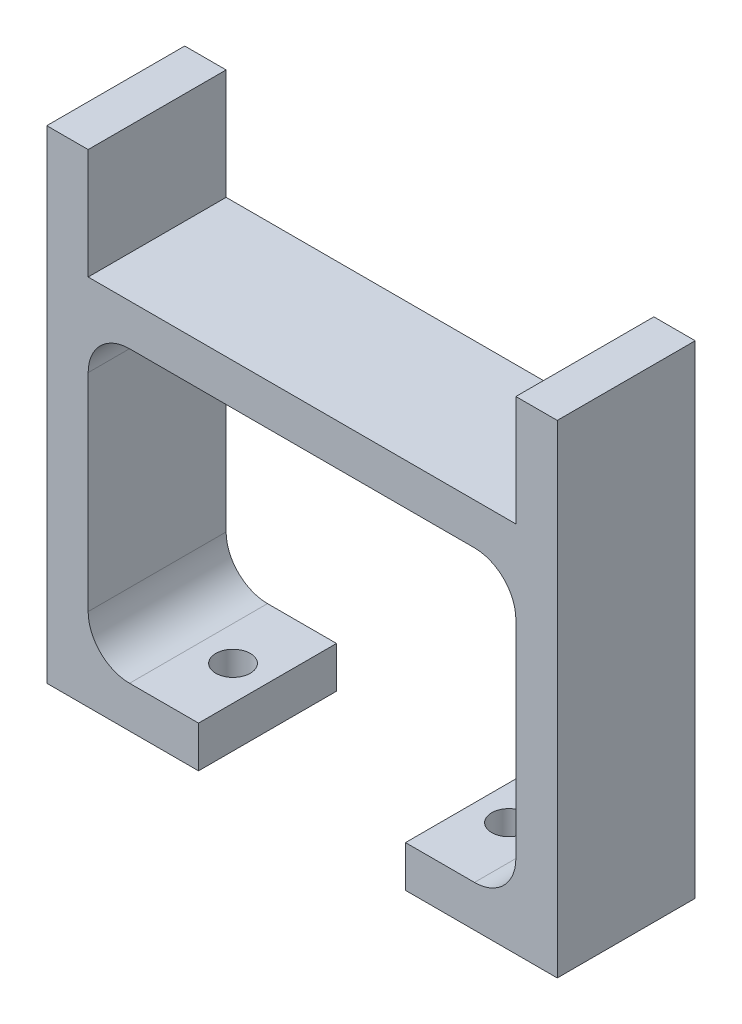
SolidWorks part; units mm, degrees
ref_plane "Front Plane" through (0, 0, 0) normal (0, 0, 1) x (1, 0, 0)
ref_plane "Top Plane" through (0, 0, 0) normal (0, 1, 0) x (1, 0, 0)
ref_plane "Right Plane" through (0, 0, 0) normal (1, 0, 0) x (0, 0, -1)
sketch "Sketch1" plane through (0, 0, 0) normal (0, 0, 1) x (1, 0, 0)
  line L0 (-15.5, 27) -> (15.5, 27)
  line L1 (15.5, 27) -> (15.5, 35)
  line L2 (15.5, 35) -> (18.5, 35)
  line L3 (18.5, 35) -> (18.5, 0)
  line L4 (18.5, 0) -> (7.5, 0)
  line L5 (7.5, 0) -> (7.5, 3)
  line L6 (7.5, 3) -> (12.5, 3)
  line L7 (15.5, 6) -> (15.5, 21)
  line L8 (12.5, 24) -> (-12.5, 24)
  line L9 (-15.5, 21) -> (-15.5, 6)
  line L10 (-12.5, 3) -> (-7.5, 3)
  line L11 (-7.5, 3) -> (-7.5, 0)
  line L12 (-7.5, 0) -> (-18.5, 0)
  line L13 (-18.5, 0) -> (-18.5, 35)
  line L14 (-18.5, 35) -> (-15.5, 35)
  line L15 (-15.5, 35) -> (-15.5, 27)
  line L16 (-15.5, 3) -> (15.5, 24) construction
  line L17 (-15.5, 24) -> (15.5, 3) construction
  arc A0 (15.5, 6) -> (12.5, 3) centre (12.5, 6) cw
  arc A1 (-12.5, 3) -> (-15.5, 6) centre (-12.5, 6) cw
  arc A2 (15.5, 21) -> (12.5, 24) centre (12.5, 21) ccw
  arc A3 (-15.5, 21) -> (-12.5, 24) centre (-12.5, 21) cw
  point P15 (0, 24)
  dimension "D8" = 3
  dimension "D1" = 31
  dimension "D2" = 3
  dimension "D3" = 3
  dimension "D4" = 3
  dimension "D5" = 3
  dimension "D6" = 8
  dimension "D7" = 24
  dimension "D9" = 5
extrude "Boss-Extrude1" add sketch "Sketch1" along normal blind 10
sketch "Sketch2" plane through (0, 3, 0) normal (0, 1, 0) x (1, 0, 0)
  line L0 (-7.5, -10) -> (-7.5, 0) construction
  line L1 (-7.5, 0) -> (-12.5, 0) construction
  line L2 (12.5, 0) -> (7.5, 0) construction
  line L3 (7.5, -10) -> (7.5, 0) construction
  circle A0 centre (-10, -5) radius 1.25
  circle A1 centre (10, -5) radius 1.25
  point P4 (-7.5, -5)
  point P7 (-10, 0)
  point P10 (0, 0)
  point P13 (10, 0)
  point P16 (7.5, -5)
  dimension "D1" = 2.5
  dimension "D2" = 2.5
extrude "Cut-Extrude1" cut sketch "Sketch2" against normal through all
